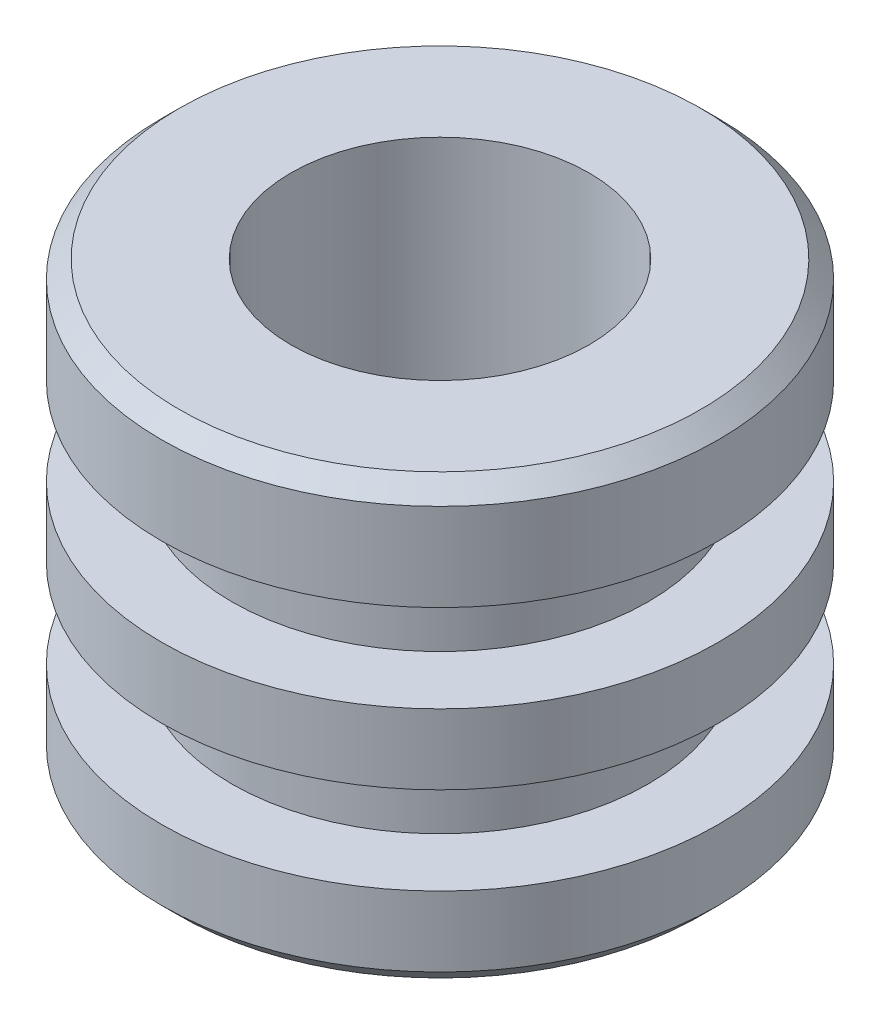
SolidWorks part; units mm, degrees
ref_plane "Alzado" through (0, 0, 0) normal (0, 0, 1) x (1, 0, 0)
ref_plane "Planta" through (0, 0, 0) normal (0, 1, 0) x (1, 0, 0)
ref_plane "Vista lateral" through (0, 0, 0) normal (1, 0, 0) x (0, 0, -1)
sketch "Croquis1" plane through (0, 0, 0) normal (0, 0, 1) x (1, 0, 0)
  line L0 (0, 22.6862) -> (0, -71.5202) construction
  line L1 (6.5, -10) -> (6.5, -0.5)
  line L2 (6.5, -0.5) -> (8.5, -0.5)
  line L3 (8.5, 15) -> (8.5, -0.5)
  line L5 (8.5, 15) -> (14.875, 15)
  line L6 (15.875, 14) -> (15.875, 9)
  line L7 (15.875, 9) -> (11.875, 9)
  line L8 (11.875, 9) -> (11.875, 4)
  line L9 (11.875, 4) -> (15.875, 4)
  line L10 (15.875, 4) -> (15.875, 0)
  line L11 (15.875, 0) -> (11.875, 0)
  line L12 (11.875, 0) -> (11.875, -5)
  line L13 (11.875, -5) -> (15.875, -5)
  line L14 (15.875, -5) -> (15.875, -9)
  line L15 (14.875, -10) -> (6.5, -10)
  line L16 (14.875, 15) -> (15.875, 14)
  line L17 (15.875, -9) -> (14.875, -10)
  point P9 (15.875, 15)
  point P18 (15.875, -10)
  dimension "D1" = 6.5
  dimension "D2" = 9.5
  dimension "D4" = 15.5
  dimension "D5" = 15.875
  dimension "D6" = 8.5
  dimension "D7" = 6
  dimension "D8" = 4
  dimension "D9" = 5
  dimension "D10" = 4
  dimension "D11" = 5
  dimension "D12" = 5
  dimension "D13" = 4
  dimension "D14" = 4
revolve "Revolución4" add sketch "Croquis1" angle 360 about L0
